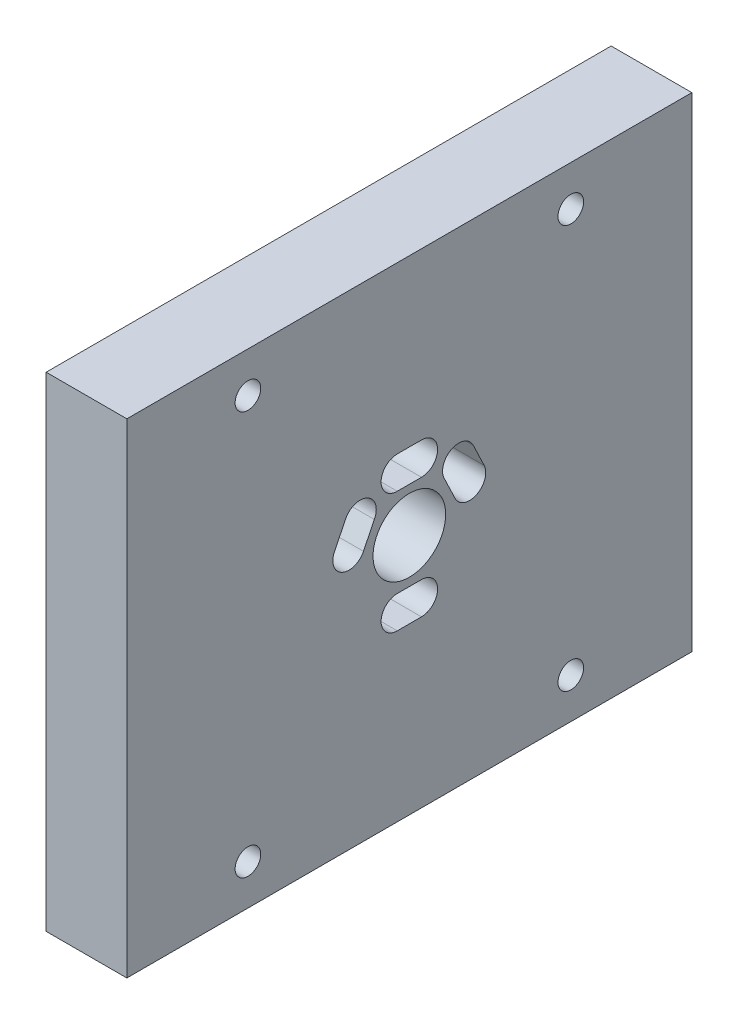
SolidWorks part; units mm, degrees
ref_plane "Front Plane" through (0, 0, 0) normal (0, 0, 1) x (1, 0, 0)
ref_plane "Top Plane" through (0, 0, 0) normal (0, 1, 0) x (1, 0, 0)
ref_plane "Right Plane" through (0, 0, 0) normal (1, 0, 0) x (0, 0, -1)
sketch "Sketch1" plane through (0, 0, 0) normal (1, 0, 0) x (0, 0, -1)
  line L9 (-31.1868, 57.8975) -> (38.8132, 57.8975)
  line L10 (-31.1868, 57.8975) -> (-31.1868, -2.1025)
  line L11 (-31.1868, -2.1025) -> (38.8132, -2.1025)
  line L12 (38.8132, 57.8975) -> (38.8132, -2.1025)
  circle A0 centre (-16.1868, 52.8975) radius 1.5875
  circle A1 centre (-16.1868, 2.8975) radius 1.5875
  circle A2 centre (23.8132, 2.8975) radius 1.5875
  circle A3 centre (23.8132, 52.8975) radius 1.5875
  line B0 (-5.4644, 30.7753) -> (-4.0816, 33.6063)
  line B1 (5.3132, 18.3975) -> (2.3132, 18.3975)
  line B2 (-0.5284, 31.7706) -> (-1.8696, 29.0208)
  line B3 (2.3132, 22.3975) -> (5.3132, 22.3975)
  line B4 (5.3132, 33.3742) -> (2.3132, 33.3742)
  line B5 (9.472, 29.0382) -> (8.081, 31.9616)
  line B6 (2.3132, 37.3742) -> (5.3132, 37.3742)
  line B7 (11.7336, 33.5893) -> (13.0834, 30.7583)
  circle B8 centre (3.8132, 27.8975) radius 4.5
  arc B9 (9.472, 29.0382) -> (13.0834, 30.7583) centre (11.2777, 29.8983) ccw
  arc B10 (11.7336, 33.5893) -> (8.081, 31.9616) centre (9.9281, 32.729) ccw
  arc B11 (-5.4644, 30.7753) -> (-1.8696, 29.0208) centre (-3.6672, 29.8975) ccw
  arc B12 (-0.5284, 31.7706) -> (-4.0816, 33.6063) centre (-2.2872, 32.7228) ccw
  arc B13 (2.3132, 37.3742) -> (2.3132, 33.3742) centre (2.3132, 35.3742) ccw
  arc B14 (5.3132, 33.3742) -> (5.3132, 37.3742) centre (5.3132, 35.3742) ccw
  arc B15 (2.3132, 22.3975) -> (2.3132, 18.3975) centre (2.3132, 20.3975) ccw
  arc B16 (5.3132, 18.3975) -> (5.3132, 22.3975) centre (5.3132, 20.3975) ccw
  dimension "D5" = 3.175
  dimension "D1" = 70
  dimension "D2" = 60
  dimension "D3" = 30
  dimension "D4" = 35
  dimension "D6" = 5
  dimension "D7" = 15
  dimension "D9" = 15
  dimension "D10" = 5
  dimension "D12" = 15
  dimension "D13" = 5
  dimension "D15" = 5
  dimension "D16" = 15
sketch_block_instance "Block1-1"
sketch_block "Block1"
extrude "Boss-Extrude1" add sketch "Sketch1" along normal blind 10
